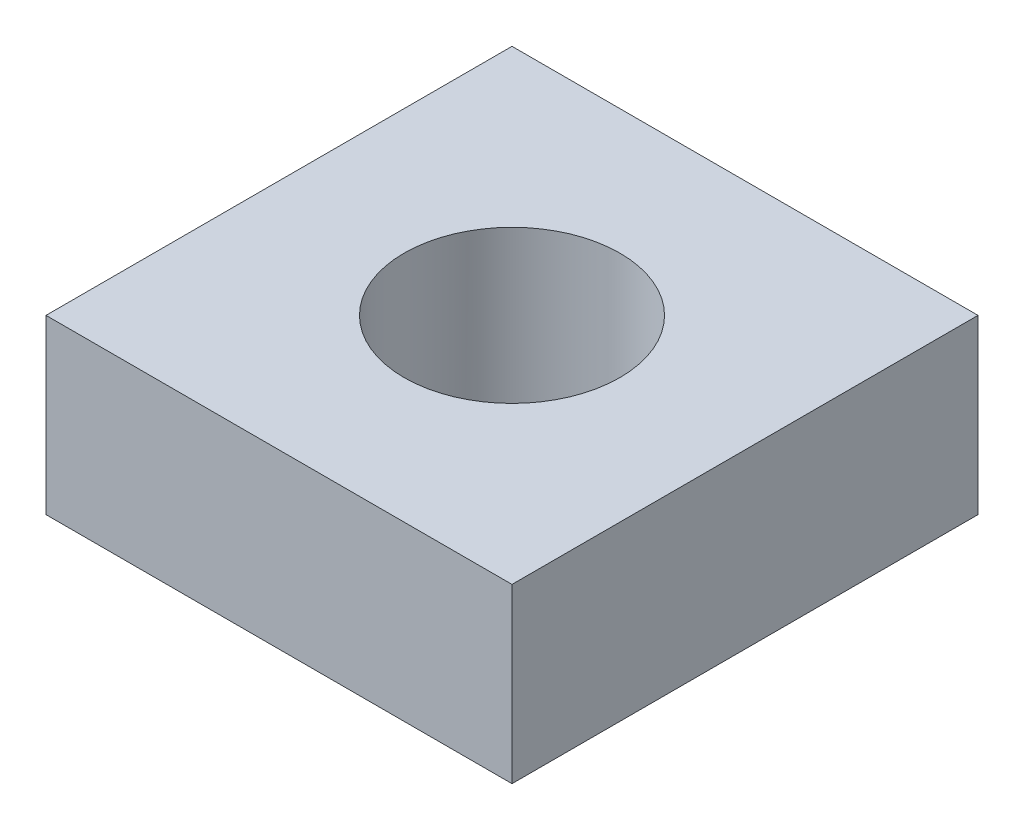
SolidWorks part; units mm, degrees
ref_plane "前视基准面" through (0, 0, 0) normal (0, 0, 1) x (1, 0, 0)
ref_plane "上视基准面" through (0, 0, 0) normal (0, 1, 0) x (1, 0, 0)
ref_plane "右视基准面" through (0, 0, 0) normal (1, 0, 0) x (0, 0, -1)
sketch "草图1" plane through (0, 0, 0) normal (0, 1, 0) x (1, 0, 0)
  line L0 (0, 9.4423) -> (0, -11.83) construction
  line L1 (-19.8976, 0) -> (17.4375, 0) construction
  line L3 (-2.7, 2.7) -> (2.7, 2.7)
  line L4 (-2.7, 2.7) -> (-2.7, -2.7)
  line L5 (-2.7, -2.7) -> (2.7, -2.7)
  line L6 (2.7, 2.7) -> (2.7, -2.7)
  line L7 (-2.7, 2.7) -> (2.7, -2.7) construction
  line L8 (-2.7, -2.7) -> (2.7, 2.7) construction
  point P5 (0, 0)
  dimension "D1" = 5.4
extrude "凸台-拉伸1" add sketch "草图1" along normal blind 2
hole_wizard "M3 螺纹孔1" positions "草图2" profile "草图3" tap size "M3" standard "GB"
sketch "草图2" plane through (0, 0, 0) normal (0, -1, 0) x (-1, 0, 0)
  point P0 (0, 0)
sketch "草图3" plane through (0, 0, 0) normal (1, 0, 0) x (0, 0, -1)
  line L0 (0, 0) -> (0, 7.2511)
  line L1 (0, 7.2511) -> (1.25, 6.5)
  line L2 (1.25, 6.5) -> (1.25, 0)
  line L5 (1.25, 0) -> (0, 0)
  line L10 (0, 7.2511) -> (-1.25, 6.5) construction
  line L11 (0, -6.35) -> (0, 107.95) construction
  dimension "螺纹孔钻头直径" = 2.5
  dimension "螺纹孔钻头深度" = 6.5
  dimension "导头角度" = 118
cosmetic thread "孔螺蚊线1"
